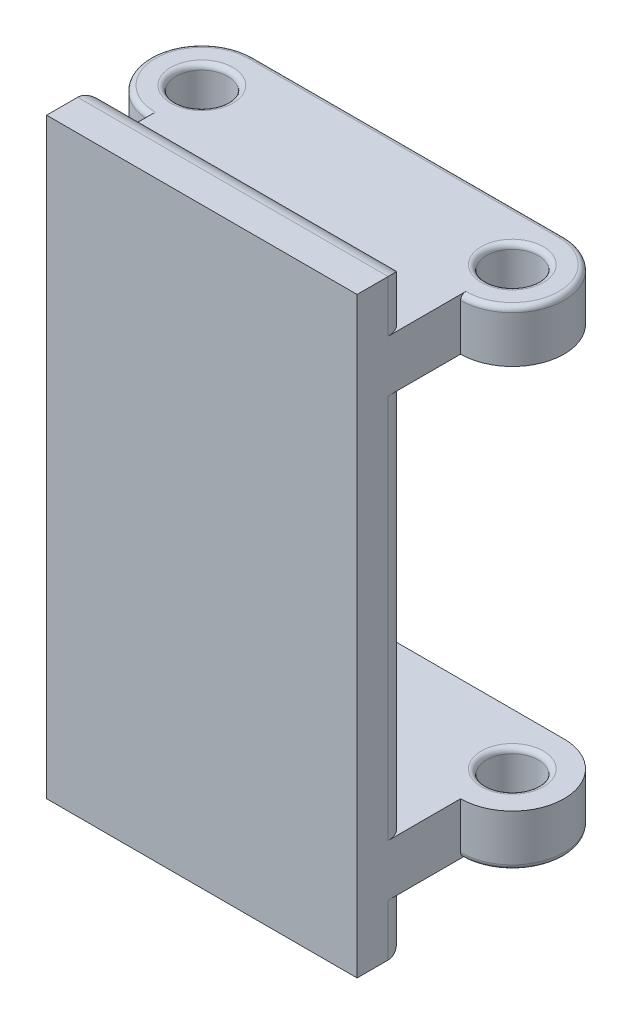
SolidWorks part; units mm, degrees
ref_plane "Front Plane" through (0, 0, 0) normal (0, 0, 1) x (1, 0, 0)
ref_plane "Top Plane" through (0, 0, 0) normal (0, 1, 0) x (1, 0, 0)
ref_plane "Right Plane" through (0, 0, 0) normal (1, 0, 0) x (0, 0, -1)
sketch "Sketch1" plane through (0, 0, 0) normal (0, 0, 1) x (1, 0, 0)
  line L1 (0, 0) -> (30, 0)
  line L2 (0, 0) -> (0, 57.2)
  line L3 (0, 57.2) -> (30, 57.2)
  line L4 (30, 0) -> (30, 57.2)
  dimension "D1" = 30
  dimension "D2" = 57.2
extrude "Boss-Extrude2" add sketch "Sketch1" along normal blind 5
ref_plane "Plane1" through (0, 10, 0) normal (0, 1, 0) x (1, 0, 0)
ref_plane "Plane2" through (0, 47.2, 0) normal (0, 1, 0) x (1, 0, 0)
ref_plane "Plane3" through (0, 28.6, 0) normal (0, 1, 0) x (1, 0, 0)
sketch "Sketch3" plane through (0, 10, 0) normal (0, 1, 0) x (1, 0, 0)
  line L0 (30, 10) -> (0, 10) construction
  line L2 (30, 15) -> (0, 15)
  line L4 (30, -5) -> (30, 10.0116) construction
  line L5 (30, 0) -> (0, 0) construction
  line L6 (0, 5) -> (0, 0)
  line L7 (0, 0) -> (30, 0)
  line L8 (30, 0) -> (30, 5)
  arc A0 (30, 5) -> (30, 15) centre (30, 10) ccw
  arc A1 (0, 15) -> (0, 5) centre (0, 10) ccw
  circle A2 centre (30, 10) radius 2.5
  circle A3 centre (0, 10) radius 2.5
  point P2 (15, 10)
  dimension "D1" = 5
  dimension "D2" = 5
  dimension "D3" = 5
  dimension "D4" = 5
extrude "Boss-Extrude3" add sketch "Sketch3" against normal blind 5
mirror "Mirror1" about plane through (0, 28.6, 0) normal (0, 1, 0) of "Boss-Extrude3"
fillet "Fillet1" radius 0.5 14 edges at (35, 5, -10) (-5, 5, -10) (35, 52.2, -10) (-5, 52.2, -10) (30, 47.2, -7.5) (0, 47.2, -7.5) (30, 10, -7.5) (0, 10, -7.5) (30, 5, -7.5) (0, 5, -7.5) (15, 5, -15) (30, 52.2, -7.5) (0, 52.2, -7.5) (15, 52.2, -15)
fillet "Fillet2" radius 2 8 edges at (15, 0, 0) (15, 57.2, 0) (0, 2.5, 0) (30, 2.5, 0) (30, 54.7, 0) (0, 54.7, 0) (30, 28.6, 0) (0, 28.6, 0)
